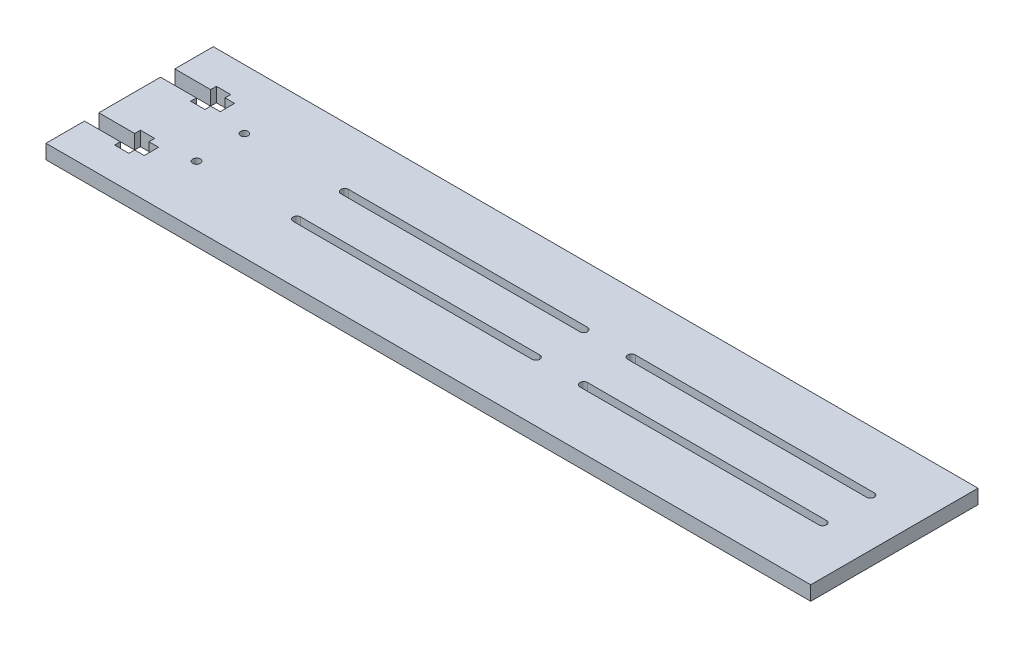
SolidWorks part; units mm, degrees
ref_plane "Front Plane" through (0, 0, 0) normal (0, 0, 1) x (1, 0, 0)
ref_plane "Top Plane" through (0, 0, 0) normal (0, 1, 0) x (1, 0, 0)
ref_plane "Right Plane" through (0, 0, 0) normal (1, 0, 0) x (0, 0, -1)
sketch "Sketch1" plane through (0, 0, 0) normal (0, 1, 0) x (1, 0, 0)
  line L1 (-160, -35) -> (160, -35)
  line L2 (-160, -35) -> (-160, 35)
  line L3 (-160, 35) -> (160, 35)
  line L4 (160, -35) -> (160, 35)
  line L5 (-160, -35) -> (160, 35) construction
  line L6 (-160, 35) -> (160, -35) construction
  point P0 (0, 0)
  dimension "D1" = 320
  dimension "D2" = 70
extrude "Boss-Extrude1" add sketch "Sketch1" along normal blind 6
sketch "Sketch3" plane through (0, 6, 0) normal (0, 1, 0) x (1, 0, 0)
  line L0 (-160, 0) -> (-135, 0) construction
  line L1 (-160, 35) -> (-160, -35) construction
  line L2 (-160, 15.9) -> (-135, 15.9) construction
  line L7 (-160, 12.9) -> (-145, 12.9)
  line L8 (-160, 18.9) -> (-145, 18.9)
  line L9 (-160, 12.9) -> (-160, 18.9)
  line L10 (-135, 12.9) -> (-135, 18.9)
  line L18 (-145, 10.5) -> (-139, 10.5)
  line L19 (-145, 10.5) -> (-145, 12.9)
  line L20 (-145, 21.3) -> (-139, 21.3)
  line L21 (-139, 10.5) -> (-139, 12.9)
  line L22 (-145, 10.5) -> (-139, 21.3) construction
  line L23 (-145, 21.3) -> (-139, 10.5) construction
  line L29 (-139, 18.9) -> (-139, 21.3)
  line L30 (-139, 18.9) -> (-135, 18.9)
  line L31 (-160, 18.9) -> (-135, 18.9) construction
  line L32 (-139, 12.9) -> (-135, 12.9)
  line L33 (-160, 12.9) -> (-135, 12.9) construction
  line L34 (-145, 18.9) -> (-145, 21.3)
  line L35 (-145, -21.3) -> (-139, -10.5) construction
  line L36 (-145, -10.5) -> (-139, -21.3) construction
  line L37 (-160, -15.9) -> (-135, -15.9) construction
  line L38 (-145, -18.9) -> (-145, -21.3)
  line L39 (-139, -12.9) -> (-135, -12.9)
  line L40 (-139, -18.9) -> (-135, -18.9)
  line L41 (-139, -18.9) -> (-139, -21.3)
  line L42 (-139, -10.5) -> (-139, -12.9)
  line L43 (-145, -21.3) -> (-139, -21.3)
  line L44 (-145, -10.5) -> (-145, -12.9)
  line L45 (-145, -10.5) -> (-139, -10.5)
  line L46 (-135, -12.9) -> (-135, -18.9)
  line L47 (-160, -12.9) -> (-160, -18.9)
  line L48 (-160, -18.9) -> (-145, -18.9)
  line L49 (-160, -12.9) -> (-145, -12.9)
  point P11 (-142, 15.9)
  point P47 (-142, -15.9)
  dimension "D3" = 15
  dimension "D4" = 15.9
  dimension "D7" = 25
  dimension "D1" = 10.8
  dimension "D2" = 6
  dimension "D5" = 3
  dimension "D6" = 3
extrude "Cut-Extrude2" cut sketch "Sketch3" against normal through all
sketch "Sketch5" plane through (0, 6, 0) normal (0, 1, 0) x (1, 0, 0)
  line L0 (40, -10) -> (140, -10) construction
  line L1 (40, -8.4) -> (140, -8.4)
  line L2 (40, -11.6) -> (140, -11.6)
  line L3 (-80, -10) -> (20, -10) construction
  line L4 (-80, -8.4) -> (20, -8.4)
  line L5 (-80, -11.6) -> (20, -11.6)
  line L6 (-80, 10) -> (20, 10) construction
  line L7 (-80, 11.6) -> (20, 11.6)
  line L8 (-80, 8.4) -> (20, 8.4)
  line L9 (40, 10) -> (140, 10) construction
  line L10 (40, 11.6) -> (140, 11.6)
  line L11 (40, 8.4) -> (140, 8.4)
  line L12 (160, -35) -> (160, 35) construction
  line L13 (-160, -35) -> (160, -35) construction
  arc A0 (40, -8.4) -> (40, -11.6) centre (40, -10) ccw
  arc A1 (140, -11.6) -> (140, -8.4) centre (140, -10) ccw
  arc A2 (-80, -8.4) -> (-80, -11.6) centre (-80, -10) ccw
  arc A3 (20, -11.6) -> (20, -8.4) centre (20, -10) ccw
  arc A4 (-80, 11.6) -> (-80, 8.4) centre (-80, 10) ccw
  arc A5 (20, 8.4) -> (20, 11.6) centre (20, 10) ccw
  arc A6 (40, 11.6) -> (40, 8.4) centre (40, 10) ccw
  arc A7 (140, 8.4) -> (140, 11.6) centre (140, 10) ccw
  point P3 (90, -10)
  point P12 (-30, -10)
  point P19 (-30, 10)
  point P26 (90, 10)
  dimension "D2" = 3.2
  dimension "D1" = 100
  dimension "D5" = 20
  dimension "D6" = 25
  dimension "D3" = 2
  dimension "D4" = 2
extrude "Cut-Extrude3" cut sketch "Sketch5" against normal through all
sketch "Sketch6" plane through (0, 0, 0) normal (0, -1, 0) x (1, 0, 0)
  circle A0 centre (-122, -10) radius 1.6 construction
  circle A1 centre (-122, 10) radius 1.6 construction
  circle A2 centre (-122, -10) radius 1.6
  circle A3 centre (-122, 10) radius 1.6
extrude "Cut-Extrude4" cut sketch "Sketch6" against normal through all
